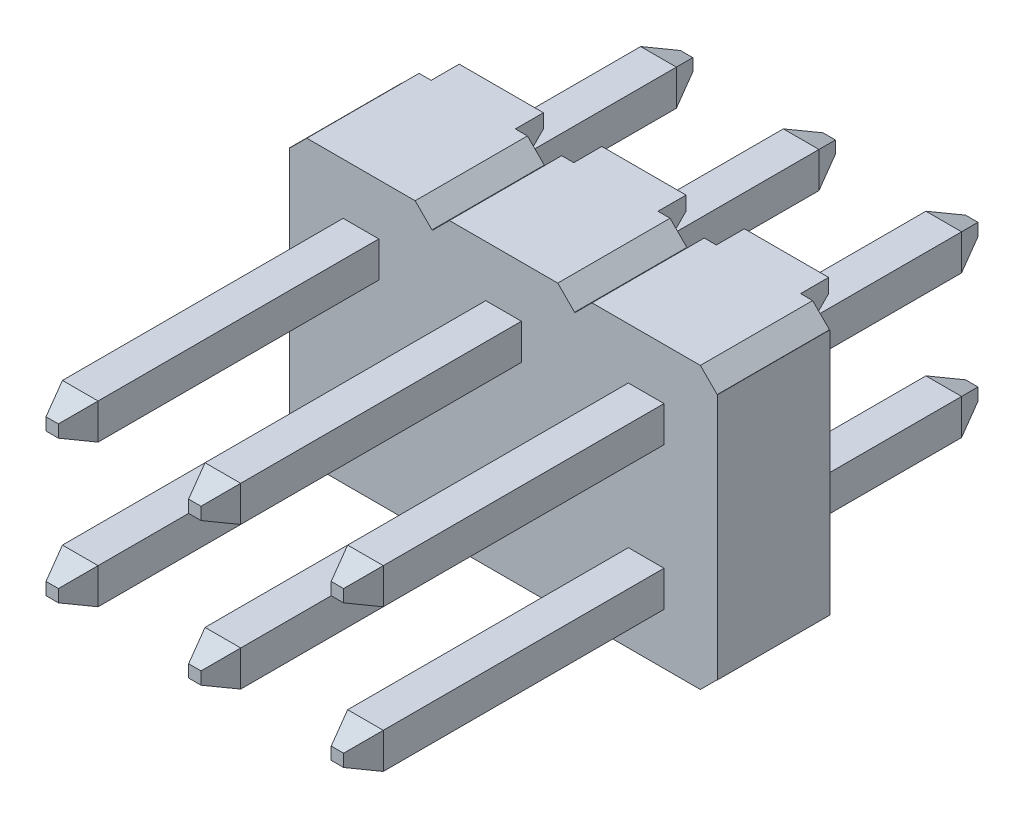
SolidWorks part; units mm, degrees
ref_plane "Front Plane" through (0, 0, 0) normal (0, 0, 1) x (1, 0, 0)
ref_plane "Top Plane" through (0, 0, 0) normal (0, 1, 0) x (1, 0, 0)
ref_plane "Right Plane" through (0, 0, 0) normal (1, 0, 0) x (0, 0, -1)
ref_plane "Plane1" through (0, 0, 0) normal (0, 0, -1) x (-1, 0, 0)
sketch "Sketch1" plane through (0, 0, 0) normal (0, 0, -1) x (-1, 0, 0)
  line L0 (-7.62, 5) -> (-7.62, 0)
  line L1 (-7.62, 0) -> (0, 0)
  line L2 (0, 0) -> (0, 5)
  line L3 (0, 5) -> (-7.62, 5)
extrude "Boss-Extrude1" add sketch "Sketch1" against normal blind 2
sketch "Sketch2" plane through (0, 0, 2) normal (0, 0, 1) x (1, 0, 0)
  line L0 (7.315, 0.3) -> (7.315, 0)
  line L1 (7.315, 0) -> (7.62, 0)
  line L2 (7.62, 0) -> (7.62, 0.3)
  line L3 (7.62, 0.3) -> (7.315, 0.3)
extrude "Cut-Extrude1" cut sketch "Sketch2" against normal through all
sketch "Sketch3" plane through (0, 0, 2) normal (0, 0, 1) x (1, 0, 0)
  line L0 (4.775, 0) -> (5.385, 0)
  line L1 (5.385, 0) -> (5.385, 0.61)
  line L2 (5.385, 0.61) -> (4.775, 0)
extrude "Cut-Extrude2" cut sketch "Sketch3" against normal through all
sketch "Sketch4" plane through (0, 0, 2) normal (0, 0, 1) x (1, 0, 0)
  line L0 (2.235, 0) -> (2.845, 0)
  line L1 (2.845, 0) -> (2.235, 0.61)
  line L2 (2.235, 0.61) -> (2.235, 0)
extrude "Cut-Extrude3" cut sketch "Sketch4" against normal through all
sketch "Sketch5" plane through (0, 0, 2) normal (0, 0, 1) x (1, 0, 0)
  line L0 (0.305, 0) -> (0.305, 0.3)
  line L1 (0.305, 0.3) -> (0, 0.3)
  line L2 (0, 0.3) -> (0, 0)
  line L3 (0, 0) -> (0.305, 0)
extrude "Cut-Extrude4" cut sketch "Sketch5" against normal blind 2
sketch "Sketch6" plane through (0, 0, 2) normal (0, 0, 1) x (1, 0, 0)
  line L0 (0.305, 4.7) -> (0.305, 5)
  line L1 (0.305, 5) -> (0, 5)
  line L2 (0, 5) -> (0, 4.7)
  line L3 (0, 4.7) -> (0.305, 4.7)
extrude "Cut-Extrude5" cut sketch "Sketch6" against normal through all
sketch "Sketch7" plane through (0, 0, 2) normal (0, 0, 1) x (1, 0, 0)
  line L0 (2.845, 5) -> (2.235, 5)
  line L1 (2.235, 5) -> (2.235, 4.39)
  line L2 (2.235, 4.39) -> (2.845, 5)
extrude "Cut-Extrude6" cut sketch "Sketch7" against normal through all
sketch "Sketch8" plane through (0, 0, 2) normal (0, 0, 1) x (1, 0, 0)
  line L0 (5.385, 5) -> (4.775, 5)
  line L1 (4.775, 5) -> (5.385, 4.39)
  line L2 (5.385, 4.39) -> (5.385, 5)
extrude "Cut-Extrude7" cut sketch "Sketch8" against normal through all
sketch "Sketch9" plane through (0, 0, 2) normal (0, 0, 1) x (1, 0, 0)
  line L0 (7.315, 5) -> (7.315, 4.7)
  line L1 (7.315, 4.7) -> (7.62, 4.7)
  line L2 (7.62, 4.7) -> (7.62, 5)
  line L3 (7.62, 5) -> (7.315, 5)
extrude "Cut-Extrude8" cut sketch "Sketch9" against normal blind 2
sketch "Sketch10" plane through (0, 0, 0) normal (0, 0, -1) x (-1, 0, 0)
  line L0 (-6.6675, 4.0875) -> (-6.0325, 4.0875)
  line L1 (-6.0325, 4.0875) -> (-6.0325, 3.4525)
  line L2 (-6.0325, 3.4525) -> (-6.6675, 3.4525)
  line L3 (-6.6675, 3.4525) -> (-6.6675, 4.0875)
extrude "Boss-Extrude2" add sketch "Sketch10" along normal blind 3.8
sketch "Sketch11" plane through (0, 0, 0) normal (0, 0, -1) x (-1, 0, 0)
  line L0 (-6.6675, 0.9125) -> (-6.6675, 1.5475)
  line L1 (-6.6675, 1.5475) -> (-6.0325, 1.5475)
  line L2 (-6.0325, 1.5475) -> (-6.0325, 0.9125)
  line L3 (-6.0325, 0.9125) -> (-6.6675, 0.9125)
extrude "Boss-Extrude3" add sketch "Sketch11" along normal blind 3.8
sketch "Sketch12" plane through (0, 0, 0) normal (0, 0, -1) x (-1, 0, 0)
  line L0 (-4.1275, 3.4525) -> (-4.1275, 4.0875)
  line L1 (-4.1275, 4.0875) -> (-3.4925, 4.0875)
  line L2 (-3.4925, 4.0875) -> (-3.4925, 3.4525)
  line L3 (-3.4925, 3.4525) -> (-4.1275, 3.4525)
extrude "Boss-Extrude4" add sketch "Sketch12" along normal blind 3.8
sketch "Sketch13" plane through (0, 0, 0) normal (0, 0, -1) x (-1, 0, 0)
  line L0 (-4.1275, 0.9125) -> (-4.1275, 1.5475)
  line L1 (-4.1275, 1.5475) -> (-3.4925, 1.5475)
  line L2 (-3.4925, 1.5475) -> (-3.4925, 0.9125)
  line L3 (-3.4925, 0.9125) -> (-4.1275, 0.9125)
extrude "Boss-Extrude5" add sketch "Sketch13" along normal blind 3.8
sketch "Sketch14" plane through (0, 0, 0) normal (0, 0, -1) x (-1, 0, 0)
  line L0 (-0.9525, 4.0875) -> (-0.9525, 3.4525)
  line L1 (-0.9525, 3.4525) -> (-1.5875, 3.4525)
  line L2 (-1.5875, 3.4525) -> (-1.5875, 4.0875)
  line L3 (-1.5875, 4.0875) -> (-0.9525, 4.0875)
extrude "Boss-Extrude6" add sketch "Sketch14" along normal blind 3.8
sketch "Sketch15" plane through (0, 0, 0) normal (0, 0, -1) x (-1, 0, 0)
  line L0 (-7.1, 0) -> (-7.1, 0.75)
  line L1 (-7.1, 0.75) -> (-5.6, 0.75)
  line L2 (-5.6, 0.75) -> (-5.6, 0)
  line L3 (-5.6, 0) -> (-7.1, 0)
extrude "Boss-Extrude7" add sketch "Sketch15" along normal blind 0.5
sketch "Sketch16" plane through (0, 0, 0) normal (0, 0, -1) x (-1, 0, 0)
  line L0 (-4.56, 0) -> (-4.56, 0.75)
  line L1 (-4.56, 0.75) -> (-3.06, 0.75)
  line L2 (-3.06, 0.75) -> (-3.06, 0)
  line L3 (-3.06, 0) -> (-4.56, 0)
extrude "Boss-Extrude8" add sketch "Sketch16" along normal blind 0.5
sketch "Sketch17" plane through (0, 0, 0) normal (0, 0, -1) x (-1, 0, 0)
  line L0 (-2.02, 0) -> (-2.02, 0.75)
  line L1 (-2.02, 0.75) -> (-0.52, 0.75)
  line L2 (-0.52, 0.75) -> (-0.52, 0)
  line L3 (-0.52, 0) -> (-2.02, 0)
extrude "Boss-Extrude9" add sketch "Sketch17" along normal blind 0.5
sketch "Sketch18" plane through (0, 0, 0) normal (0, 0, -1) x (-1, 0, 0)
  line L0 (-0.52, 5) -> (-0.52, 4.25)
  line L1 (-0.52, 4.25) -> (-2.02, 4.25)
  line L2 (-2.02, 4.25) -> (-2.02, 5)
  line L3 (-2.02, 5) -> (-0.52, 5)
extrude "Boss-Extrude10" add sketch "Sketch18" along normal blind 0.5
sketch "Sketch19" plane through (0, 0, 0) normal (0, 0, -1) x (-1, 0, 0)
  line L0 (-3.06, 5) -> (-3.06, 4.25)
  line L1 (-3.06, 4.25) -> (-4.56, 4.25)
  line L2 (-4.56, 4.25) -> (-4.56, 5)
  line L3 (-4.56, 5) -> (-3.06, 5)
extrude "Boss-Extrude11" add sketch "Sketch19" along normal blind 0.5
sketch "Sketch20" plane through (0, 0, 0) normal (0, 0, -1) x (-1, 0, 0)
  line L0 (-5.6, 5) -> (-5.6, 4.25)
  line L1 (-5.6, 4.25) -> (-7.1, 4.25)
  line L2 (-7.1, 4.25) -> (-7.1, 5)
  line L3 (-7.1, 5) -> (-5.6, 5)
extrude "Boss-Extrude12" add sketch "Sketch20" along normal blind 0.5
sketch "Sketch21" plane through (0, 0, 0) normal (0, 0, -1) x (-1, 0, 0)
  line L0 (-1.5875, 0.9125) -> (-1.5875, 1.5475)
  line L1 (-1.5875, 1.5475) -> (-0.9525, 1.5475)
  line L2 (-0.9525, 1.5475) -> (-0.9525, 0.9125)
  line L3 (-0.9525, 0.9125) -> (-1.5875, 0.9125)
extrude "Boss-Extrude13" add sketch "Sketch21" along normal blind 3.8
sketch "Sketch22" plane through (0, 0, 2) normal (0, 0, 1) x (1, 0, 0)
  line L0 (6.0325, 4.0875) -> (6.6675, 4.0875)
  line L1 (6.6675, 4.0875) -> (6.6675, 3.4525)
  line L2 (6.6675, 3.4525) -> (6.0325, 3.4525)
  line L3 (6.0325, 3.4525) -> (6.0325, 4.0875)
extrude "Boss-Extrude14" add sketch "Sketch22" along normal blind 5.5
sketch "Sketch23" plane through (0, 0, 2) normal (0, 0, 1) x (1, 0, 0)
  line L0 (6.0325, 0.9125) -> (6.0325, 1.5475)
  line L1 (6.0325, 1.5475) -> (6.6675, 1.5475)
  line L2 (6.6675, 1.5475) -> (6.6675, 0.9125)
  line L3 (6.6675, 0.9125) -> (6.0325, 0.9125)
extrude "Boss-Extrude15" add sketch "Sketch23" along normal blind 5.5
sketch "Sketch24" plane through (0, 0, 2) normal (0, 0, 1) x (1, 0, 0)
  line L0 (3.4925, 4.0875) -> (4.1275, 4.0875)
  line L1 (4.1275, 4.0875) -> (4.1275, 3.4525)
  line L2 (4.1275, 3.4525) -> (3.4925, 3.4525)
  line L3 (3.4925, 3.4525) -> (3.4925, 4.0875)
extrude "Boss-Extrude16" add sketch "Sketch24" along normal blind 5.5
sketch "Sketch25" plane through (0, 0, 2) normal (0, 0, 1) x (1, 0, 0)
  line L0 (3.4925, 1.5475) -> (4.1275, 1.5475)
  line L1 (4.1275, 1.5475) -> (4.1275, 0.9125)
  line L2 (4.1275, 0.9125) -> (3.4925, 0.9125)
  line L3 (3.4925, 0.9125) -> (3.4925, 1.5475)
extrude "Boss-Extrude17" add sketch "Sketch25" along normal blind 5.5
sketch "Sketch26" plane through (0, 0, 2) normal (0, 0, 1) x (1, 0, 0)
  line L0 (0.9525, 4.0875) -> (1.5875, 4.0875)
  line L1 (1.5875, 4.0875) -> (1.5875, 3.4525)
  line L2 (1.5875, 3.4525) -> (0.9525, 3.4525)
  line L3 (0.9525, 3.4525) -> (0.9525, 4.0875)
extrude "Boss-Extrude18" add sketch "Sketch26" along normal blind 5.5
sketch "Sketch27" plane through (0, 0, 2) normal (0, 0, 1) x (1, 0, 0)
  line L0 (0.9525, 0.9125) -> (0.9525, 1.5475)
  line L1 (0.9525, 1.5475) -> (1.5875, 1.5475)
  line L2 (1.5875, 1.5475) -> (1.5875, 0.9125)
  line L3 (1.5875, 0.9125) -> (0.9525, 0.9125)
extrude "Boss-Extrude19" add sketch "Sketch27" along normal blind 5.5
draft "Draft1" type of draft neutral plane draft angle 45 faces to draft 2 face at (5.385, 0.305, 1) face at (7.315, 0.15, 1) neutral plane through (7.62, 0, 2) neutral plane normal (0, -1, 0) parameters "D1"=45
draft "Draft2" type of draft neutral plane draft angle 45 faces to draft 2 face at (0.305, 0.15, 1) face at (2.235, 0.305, 1) neutral plane through (7.62, 0, 2) neutral plane normal (0, -1, 0) parameters "D1"=45
draft "Draft3" type of draft neutral plane draft angle 45 faces to draft 2 face at (2.235, 4.695, 1) face at (0.305, 4.85, 1) neutral plane through (0, 5, 2) neutral plane normal (0, 1, 0) parameters "D1"=45
draft "Draft4" type of draft neutral plane draft angle 45 faces to draft 2 face at (7.315, 4.85, 1) face at (5.385, 4.695, 1) neutral plane through (0, 5, 2) neutral plane normal (0, 1, 0) parameters "D1"=45
draft "Draft5" type of draft neutral plane draft angle 45 faces to draft 6 face at (6.35, 0.75, -0.25) face at (3.81, 0.75, -0.25) face at (1.27, 0.75, -0.25) face at (1.27, 4.25, -0.25) face at (3.81, 4.25, -0.25) face at (6.35, 4.25, -0.25) neutral plane through (0, 0, 0) neutral plane normal (0, 0, -1) parameters "D1"=45
chamfer "Chamfer1" distance 0.0071 angle 45 4 edges at (5.08, 0.305, 1) (2.54, 4.695, 1) (5.08, 4.695, 1) (2.54, 0.305, 1)
chamfer "Chamfer2" distance 0.2071 angle 67.5 48 edges at (6.6675, 3.77, 7.5) (6.35, 3.4525, 7.5) (6.35, 4.0875, 7.5) (6.0325, 3.77, 7.5) (6.35, 1.5475, 7.5) (6.6675, 1.23, 7.5) (6.0325, 1.23, 7.5) (6.35, 0.9125, 7.5) (1.5875, 3.77, 7.5) (1.27, 3.4525, 7.5) (1.27, 4.0875, 7.5) (0.9525, 3.77, 7.5) (6.35, 1.5475, -3.8) (6.6675, 1.23, -3.8) (6.0325, 1.23, -3.8) (6.35, 0.9125, -3.8) (1.27, 3.4525, -3.8) (1.5875, 3.77, -3.8) (0.9525, 3.77, -3.8) (1.27, 4.0875, -3.8) (3.81, 4.0875, -3.8) (4.1275, 3.77, -3.8) (3.4925, 3.77, -3.8) (3.81, 3.4525, -3.8) (4.1275, 3.77, 7.5) (3.81, 3.4525, 7.5) (3.81, 4.0875, 7.5) (3.4925, 3.77, 7.5) (3.81, 1.5475, -3.8) (4.1275, 1.23, -3.8) (3.4925, 1.23, -3.8) (3.81, 0.9125, -3.8) (1.27, 1.5475, 7.5) (1.5875, 1.23, 7.5) (0.9525, 1.23, 7.5) (1.27, 0.9125, 7.5) (1.27, 1.5475, -3.8) (1.5875, 1.23, -3.8) (0.9525, 1.23, -3.8) (1.27, 0.9125, -3.8) (6.0325, 3.77, -3.8) (6.35, 4.0875, -3.8) (6.35, 3.4525, -3.8) (6.6675, 3.77, -3.8) (4.1275, 1.23, 7.5) (3.81, 0.9125, 7.5) (3.81, 1.5475, 7.5) (3.4925, 1.23, 7.5)
